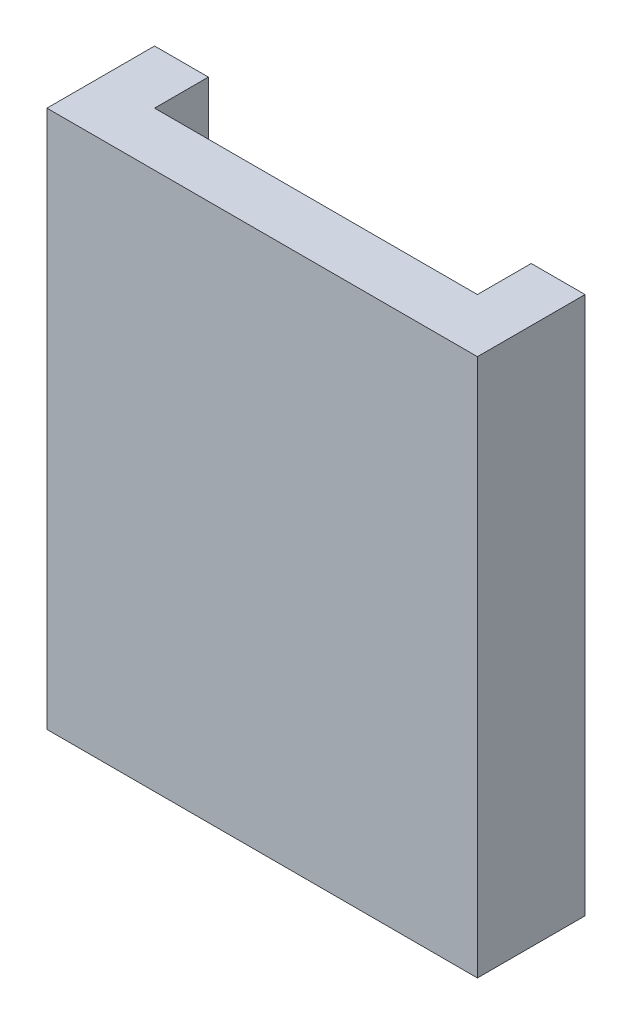
SolidWorks part; units mm, degrees
ref_plane "Front Plane" through (0, 0, 0) normal (0, 0, 1) x (1, 0, 0)
ref_plane "Top Plane" through (0, 0, 0) normal (0, 1, 0) x (1, 0, 0)
ref_plane "Right Plane" through (0, 0, 0) normal (1, 0, 0) x (0, 0, -1)
sketch "Sketch1" plane through (0, 0, 0) normal (0, 0, 1) x (1, 0, 0)
  line L1 (-40, 50) -> (40, 50)
  line L2 (-40, 50) -> (-40, -50)
  line L3 (-40, -50) -> (40, -50)
  line L4 (40, 50) -> (40, -50)
  line L5 (-40, 50) -> (40, -50) construction
  line L6 (-40, -50) -> (40, 50) construction
  point P0 (0, 0)
  dimension "D1" = 100
  dimension "D2" = 80
extrude "Boss-Extrude1" add sketch "Sketch1" along normal blind 20
sketch "Sketch2" plane through (0, 50, 0) normal (0, 1, 0) x (1, 0, 0)
  line L0 (40, 0) -> (-40, 0) construction
  line L1 (-30, 0) -> (30, 0)
  line L2 (-30, 0) -> (-30, -10)
  line L3 (-30, -10) -> (30, -10)
  line L4 (30, 0) -> (30, -10)
  line L5 (-40, -20) -> (-40, 0) construction
  line L6 (40, -20) -> (40, 0) construction
  line L7 (40, -20) -> (-40, -20) construction
  dimension "D1" = 10
  dimension "D2" = 10
  dimension "D3" = 10
extrude "Cut-Extrude1" cut sketch "Sketch2" against normal blind 100
